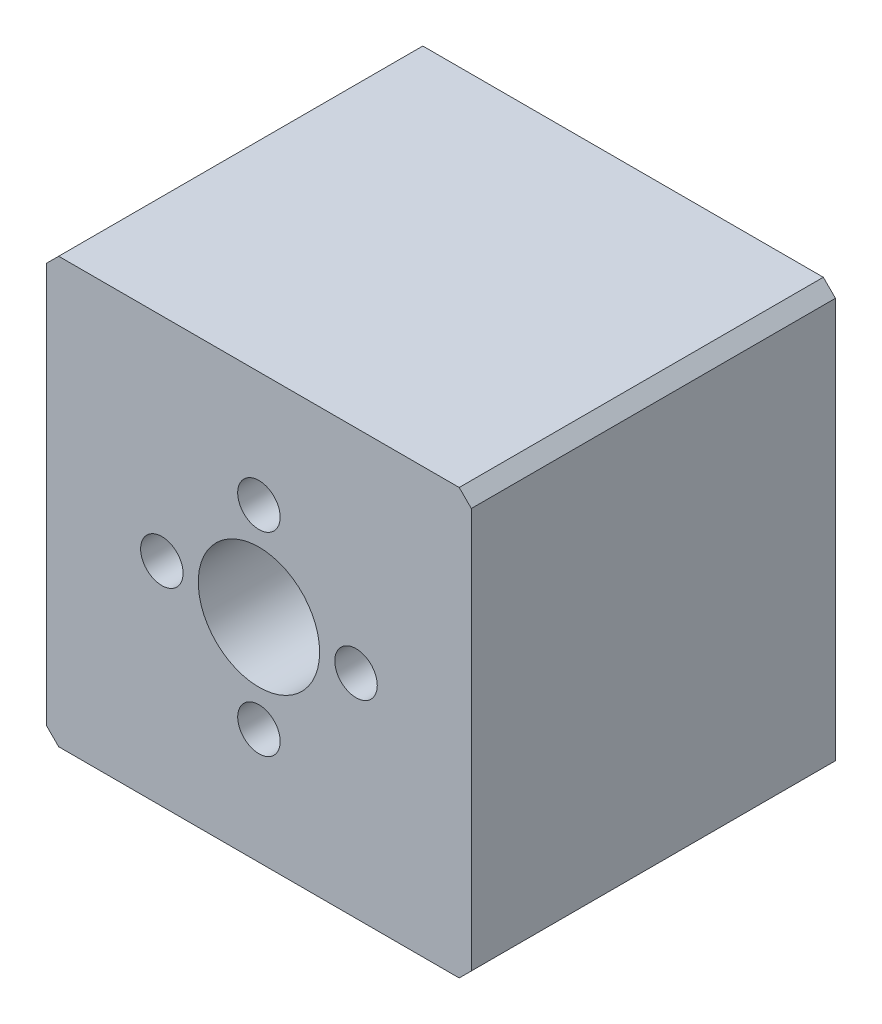
SolidWorks part; units mm, degrees
ref_plane "Front Plane" through (0, 0, 0) normal (0, 0, 1) x (1, 0, 0)
ref_plane "Top Plane" through (0, 0, 0) normal (0, 1, 0) x (1, 0, 0)
ref_plane "Right Plane" through (0, 0, 0) normal (1, 0, 0) x (0, 0, -1)
sketch "Sketch1" plane through (0, 0, 0) normal (0, 0, 1) x (1, 0, 0)
  line L0 (-17.5, 19) -> (17.5, 19)
  line L1 (17.5, 19) -> (17.5, -16)
  line L2 (17.5, -16) -> (-17.5, -16)
  line L3 (-17.5, -16) -> (-17.5, 19)
  circle A0 centre (0, 1.5) radius 5
extrude "Boss-Extrude1" add sketch "Sketch1" along normal mid plane 30
sketch "Sketch2" plane through (0, 0, 15) normal (0, 0, 1) x (1, 0, 0)
  circle A0 centre (0, 9.5) radius 1.75
  circle A1 centre (0, -6.5) radius 1.75
  circle A2 centre (8, 1.5) radius 1.75
  circle A3 centre (-8, 1.5) radius 1.75
extrude "Cut-Extrude1" cut sketch "Sketch2" against normal blind 10
chamfer "Chamfer1" distance 1 angle 45 4 edges at (-17.5, -16, 0) (17.5, -16, 0) (-17.5, 19, 0) (17.5, 19, 0)
sketch "Sketch3" plane through (0, -16, 0) normal (0, -1, 0) x (1, 0, 0)
  line L0 (19.25, 0) -> (-19.25, 0) construction
  line L1 (0, -16.5) -> (0, 16.5) construction
  circle A0 centre (12.5, 8) radius 2
  circle A1 centre (12.5, -8) radius 2
  dimension "D1" = 4
  dimension "D2" = 4
  dimension "D3" = 16
  dimension "D4" = 8
  dimension "D5" = 12.5
  dimension "D6" = 8
extrude "Cut-Extrude2" cut sketch "Sketch3" against normal blind 10
mirror "Mirror1" about plane through (0, 0, 0) normal (1, 0, 0) of "Cut-Extrude2"
